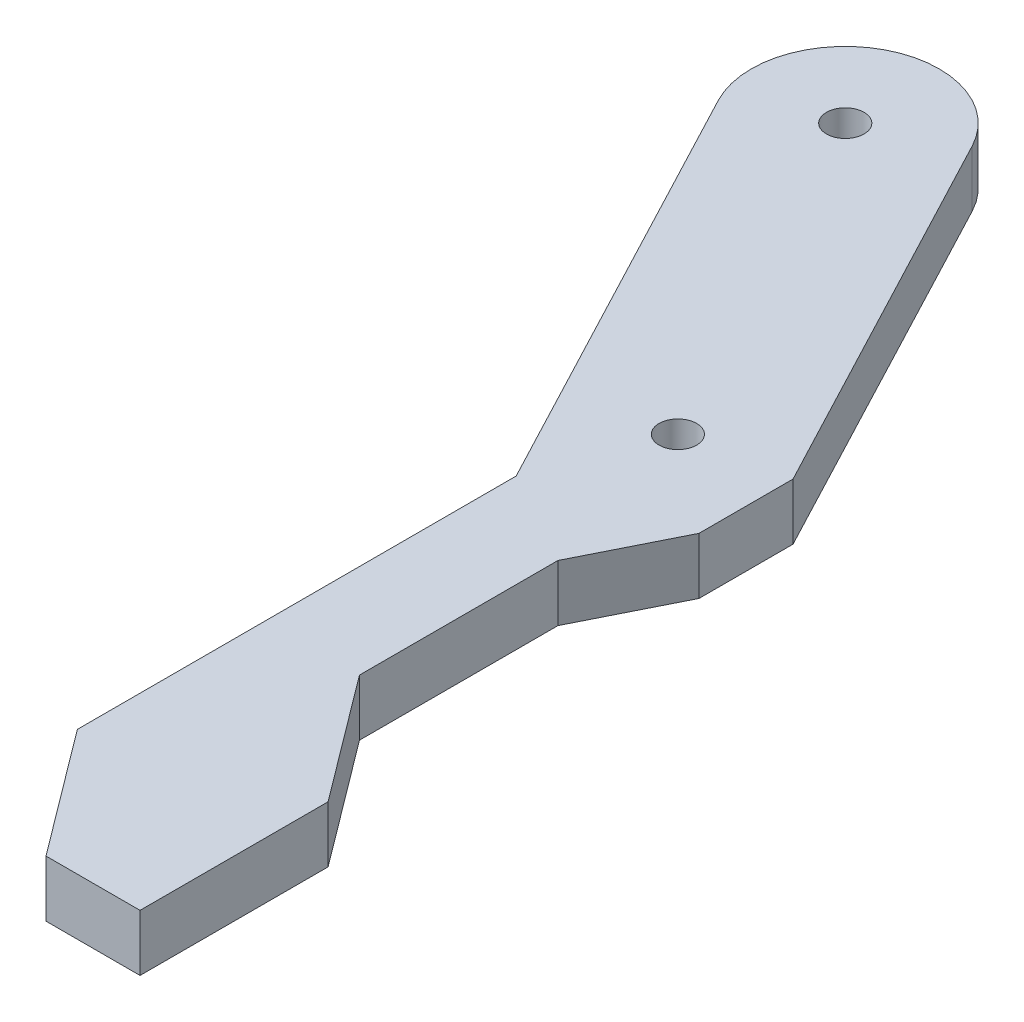
SolidWorks part; units mm, degrees
ref_plane "Alzado" through (0, 0, 0) normal (0, 0, 1) x (1, 0, 0)
ref_plane "Planta" through (0, 0, 0) normal (0, 1, 0) x (1, 0, 0)
ref_plane "Vista lateral" through (0, 0, 0) normal (1, 0, 0) x (0, 0, -1)
sketch "Croquis1" plane through (0, 0, 0) normal (0, 1, 0) x (1, 0, 0)
  line L0 (2.495, 24.5553) -> (12.3715, 5.7778) construction
  line L1 (-1.9302, 22.2277) -> (9.995, -0.4447)
  line L2 (-2.505, 24.5553) -> (-2.505, -39.1191) construction
  line L3 (6.9202, 26.8828) -> (17.495, 6.7778)
  line L4 (17.495, 6.7778) -> (17.495, 1.7778)
  line L5 (17.495, 1.7778) -> (17.495, -39.1191) construction
  line L6 (17.495, 1.7778) -> (14.995, -3.2222)
  line L7 (9.995, -0.4447) -> (9.995, -23.7781)
  line L8 (14.995, -13.7781) -> (14.995, -36.0632) construction
  line L9 (2.495, 29.5553) -> (58.6141, 29.5553) construction
  line L10 (9.995, -0.4447) -> (29.249, -0.4447) construction
  line L11 (14.995, -3.2222) -> (17.945, -3.2222) construction
  line L12 (19.498, -19.782) -> (11.498, -25.782) construction
  line L13 (17.495, 6.7778) -> (9.6002, 6.7778) construction
  line L14 (4.599, 9.8142) -> (13.4495, 14.4693) construction
  line L17 (14.995, -3.2222) -> (14.995, -13.7781)
  line L18 (14.995, -13.7781) -> (19.995, -20.4447)
  line L19 (9.995, -23.7781) -> (14.995, -30.4447)
  line L20 (14.995, -30.4447) -> (19.995, -30.4447)
  line L21 (19.995, -30.4447) -> (19.995, -20.4447)
  line L23 (19.995, -20.4447) -> (24.9172, -20.4447) construction
  line L24 (19.995, -30.4447) -> (41.1083, -30.4447) construction
  line L25 (9.995, -23.7781) -> (9.995, -40.4419) construction
  line L26 (19.995, -30.4447) -> (19.995, -40.4419) construction
  circle A0 centre (2.495, 24.5553) radius 1
  arc A1 (6.9202, 26.8828) -> (-1.9302, 22.2277) centre (2.495, 24.5553) ccw
  circle A2 centre (12.3715, 5.7778) radius 1
  dimension "D12" = 2
  dimension "D1" = 5
  dimension "D2" = 20
  dimension "D3" = 5
  dimension "D4" = 10
  dimension "D5" = 30
  dimension "D6" = 10
  dimension "D7" = 5
  dimension "D8" = 10
  dimension "D9" = 10
  dimension "D10" = 5
  dimension "D11" = 60
extrude "Saliente-Extruir1" add sketch "Croquis1" along normal blind 3
